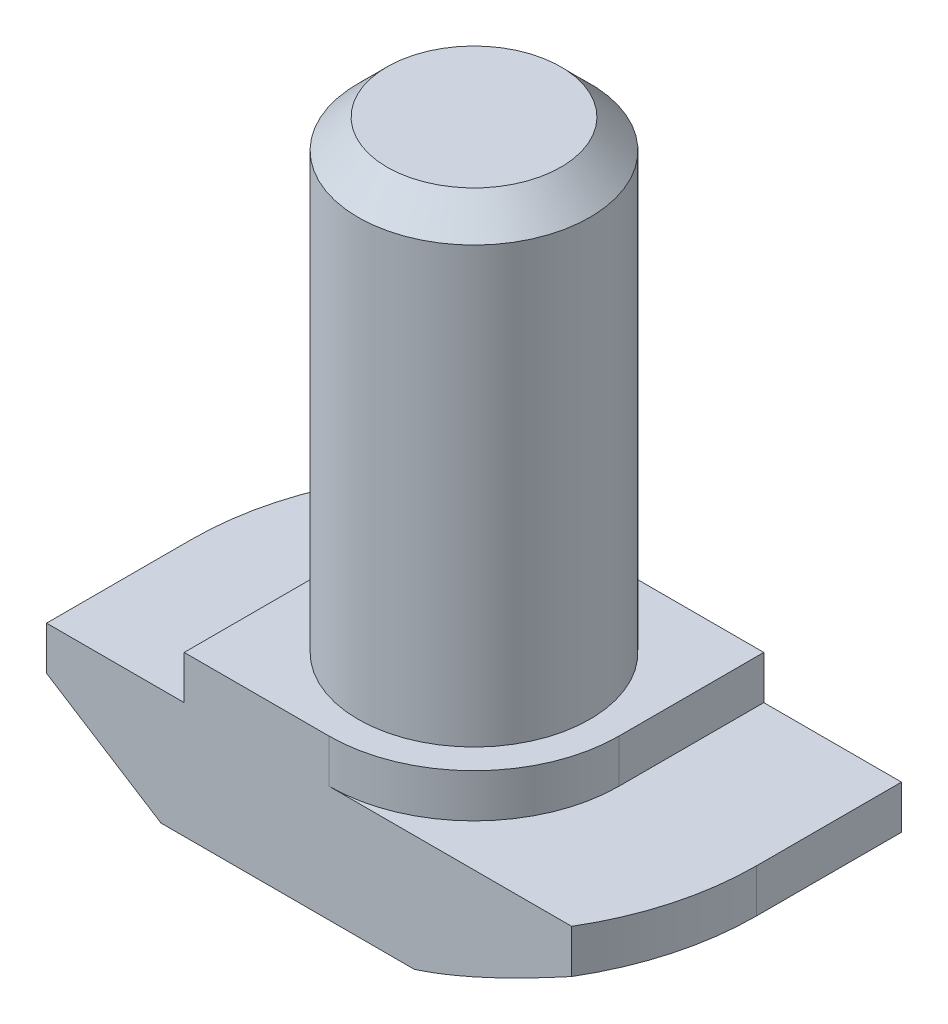
SolidWorks part; units mm, degrees
ref_plane "Спереди" through (0, 0, 0) normal (0, 0, 1) x (1, 0, 0)
ref_plane "Сверху" through (0, 0, 0) normal (0, 1, 0) x (1, 0, 0)
ref_plane "Справа" through (0, 0, 0) normal (1, 0, 0) x (0, 0, -1)
sketch "Эскиз1" plane through (0, 0, 0) normal (0, 0, 1) x (1, 0, 0)
  line L0 (9.75, 0) -> (-9.75, 0)
  line L1 (-9.75, 0) -> (-9.75, 4)
  line L2 (-9.75, 4) -> (-5, 4)
  line L3 (-5, 4) -> (-5, 5.5)
  line L4 (-5, 5.5) -> (5, 5.5)
  line L5 (0, 5.5) -> (0, 0) construction
  line L6 (5, 4) -> (5, 5.5)
  line L7 (9.75, 4) -> (5, 4)
  line L8 (9.75, 0) -> (9.75, 4)
  point P12 (-8.25, 2.6435)
  point P13 (-4, 3.6993)
  dimension "D1" = 10
  dimension "D2" = 19.5
  dimension "D3" = 5.5
  dimension "D4" = 1.5
extrude "Бобышка-Вытянуть1" add sketch "Эскиз1" along normal mid plane 10
sketch "Эскиз3" plane through (0, 5.5, 0) normal (0, 1, 0) x (1, 0, 0)
  line L1 (5, 5) -> (-5, 5) construction
  line L2 (-5, 0) -> (-5, 5)
  line L3 (-5, 5) -> (0, 5)
  line L4 (0, -5) -> (5, -5)
  line L5 (5, -5) -> (-5, -5) construction
  line L6 (5, -5) -> (5, 0)
  line L7 (5, -5) -> (5, 5) construction
  arc A0 (-5, 0) -> (0, 5) centre (0, 0) cw
  arc A1 (5, 0) -> (0, -5) centre (0, 0) cw
extrude "Вырез-Вытянуть1" cut sketch "Эскиз3" against normal up to surface (1.5 mm away) up to face at (-7.375, 4, 0)
sketch "Эскиз2" plane through (0, 5.5, 0) normal (0, 1, 0) x (1, 0, 0)
  circle A0 centre (0, 0) radius 4
  dimension "D1" = 8
extrude "Бобышка-Вытянуть2" add sketch "Эскиз2" along normal blind 16
cosmetic thread "Условное изображение резьбы1" parameters "D1"=16, "D2"=6.619
sketch "Эскиз4" plane through (0, 4, 0) normal (0, 1, 0) x (1, 0, 0)
  line L0 (-9.75, -5) -> (-9.75, 5) construction
  line L1 (9.75, -5) -> (9.75, 5) construction
  line L2 (-8.3703, 5) -> (-9.75, 5)
  line L3 (-9.75, 5) -> (-9.75, 0)
  line L4 (8.3703, -5) -> (9.75, -5)
  line L5 (9.75, -5) -> (9.75, 0)
  arc A0 (-9.75, 0) -> (-8.3703, 5) centre (0, 0) cw
  arc A1 (9.75, 0) -> (8.3703, -5) centre (0, 0) cw
extrude "Вырез-Вытянуть2" cut sketch "Эскиз4" against normal through all
sketch "Эскиз5" plane through (0, 0, 5) normal (0, 0, 1) x (1, 0, 0)
  line L0 (-9.75, 2.5) -> (-5.8, 0)
  line L1 (-9.75, 4) -> (-9.75, 0) construction
  line L2 (-9.75, 0) -> (8.3703, 0) construction
  line L3 (-5.8, 0) -> (-9.75, 0)
  line L4 (-9.75, 0) -> (-9.75, 2.5)
  line L6 (-5, 4) -> (-9.75, 4) construction
  line L7 (-5, 5.5) -> (-5, 4) construction
  point P6 (-4.9519, 0)
  point P9 (0, 0)
  point P10 (-4.6154, 0)
  point P12 (-8.25, 2.2665)
  point P15 (0, 0)
  dimension "D1" = 1.5
  dimension "D2" = 0.8
sketch "Эскиз6" plane through (0, 0, 0) normal (0, -1, 0) x (1, 0, 0)
  line L0 (0, -9.75) -> (9.75, -9.75)
  line L1 (9.75, -9.75) -> (9.75, 0)
  line L2 (0, 9.75) -> (-9.75, 9.75)
  line L3 (-9.75, 9.75) -> (-9.75, 0)
  arc A0 (-9.75, 0) -> (0, -9.75) centre (0, 0) ccw
  arc A1 (9.75, 0) -> (0, 9.75) centre (0, 0) ccw
  point P10 (0, 0)
sweep "Вырез-По траектории1" cut profiles "Эскиз5" path "Эскиз6"
chamfer "Фаска2" distance 1 angle 45 1 edges at (0, 21.5, 4)
